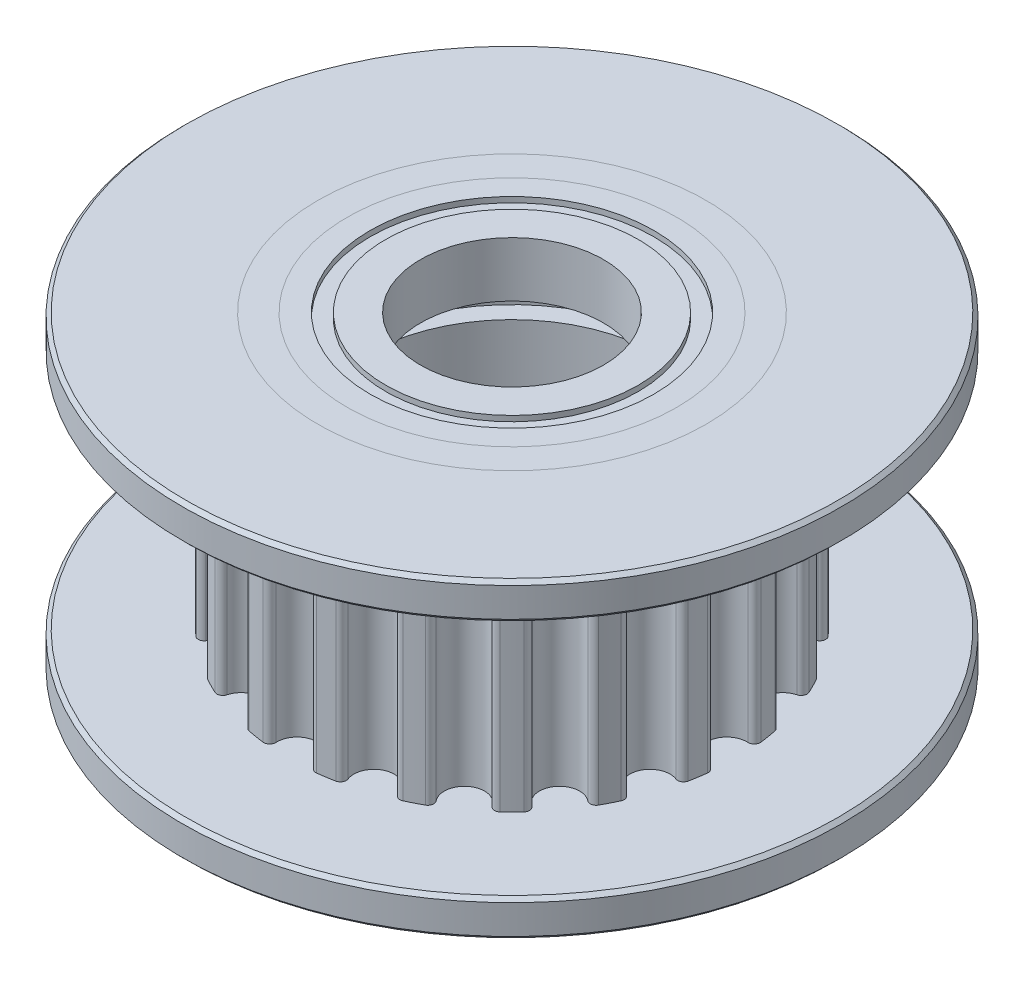
SolidWorks part; units mm, degrees
material "1060 Alloy"
ref_plane "Přední rovina" through (0, 0, 0) normal (0, 0, 1) x (1, 0, 0)
ref_plane "Horní rovina" through (0, 0, 0) normal (0, 1, 0) x (1, 0, 0)
ref_plane "Pravá rovina" through (0, 0, 0) normal (1, 0, 0) x (0, 0, -1)
sketch "Skica1" plane through (0, 0, 0) normal (0, 0, 1) x (1, 0, 0)
  line L0 (0, 0) -> (0, 8.5) construction
  line L1 (4.5, 8.5) -> (5.3, 8.5)
  line L2 (5.3, 8.5) -> (5.3, 7.5)
  line L3 (5.3, 7.5) -> (9, 7.5)
  line L4 (9, 7.5) -> (9, 1)
  line L5 (4.5, 0) -> (5.3, 0)
  line L6 (5.3, 0) -> (5.3, 1)
  line L7 (5.3, 1) -> (9, 1)
  line L8 (4.5, 3) -> (4, 3)
  line L9 (4.5, 3) -> (4.5, 0)
  line L10 (4.5, 8.5) -> (4.5, 5.5)
  line L11 (4.5, 5.5) -> (4, 5.5)
  line L12 (4, 5.5) -> (4, 3)
  dimension "D1" = 6.5
  dimension "D2" = 2.5
  dimension "D3" = 3
  dimension "D4" = 9
  dimension "D5" = 4.5
  dimension "D6" = 5.3
  dimension "D7" = 8.5
revolve "Rotovat1" add sketch "Skica1" angle 360 about L0
sketch "Skica2" plane through (0, 7.5, 0) normal (0, 1, 0) x (1, 0, 0)
  arc A0 (-0.5492, 5.8991) -> (0.5492, 5.8991) centre (0, 5.87) ccw
  arc A1 (-0.5492, 5.8991) -> (-0.7281, 6.0665) centre (-0.709, 5.9076) ccw
  arc A2 (0.7281, 6.0665) -> (0.5492, 5.8991) centre (0.709, 5.9076) ccw
  arc A3 (1.1822, 5.9945) -> (0.7281, 6.0665) centre (0, 0) ccw
  arc A4 (1.3006, 5.7801) -> (2.3453, 5.4407) centre (1.8139, 5.5827) ccw
  arc A5 (1.3006, 5.7801) -> (1.1822, 5.9945) centre (1.1512, 5.8376) ccw
  arc A6 (2.5671, 5.5446) -> (2.3453, 5.4407) centre (2.4999, 5.3994) ccw
  arc A7 (2.9768, 5.3358) -> (2.5671, 5.5446) centre (0, 0) ccw
  arc A8 (3.0231, 5.0953) -> (3.9118, 4.4497) centre (3.4503, 4.7489) ccw
  arc A9 (3.0231, 5.0953) -> (2.9768, 5.3358) centre (2.8988, 5.1961) ccw
  arc A10 (4.1548, 4.4799) -> (3.9118, 4.4497) centre (4.046, 4.3626) ccw
  arc A11 (4.4799, 4.1548) -> (4.1548, 4.4799) centre (0, 0) ccw
  arc A12 (4.4497, 3.9118) -> (5.0953, 3.0231) centre (4.7489, 3.4503) ccw
  arc A13 (4.4497, 3.9118) -> (4.4799, 4.1548) centre (4.3626, 4.046) ccw
  arc A14 (5.3358, 2.9768) -> (5.0953, 3.0231) centre (5.1961, 2.8988) ccw
  arc A15 (5.5446, 2.5671) -> (5.3358, 2.9768) centre (0, 0) ccw
  arc A16 (5.4407, 2.3453) -> (5.7801, 1.3006) centre (5.5827, 1.8139) ccw
  arc A17 (5.4407, 2.3453) -> (5.5446, 2.5671) centre (5.3994, 2.4999) ccw
  arc A18 (5.9945, 1.1822) -> (5.7801, 1.3006) centre (5.8376, 1.1512) ccw
  arc A19 (6.0665, 0.7281) -> (5.9945, 1.1822) centre (0, 0) ccw
  arc A20 (5.8991, 0.5492) -> (5.8991, -0.5492) centre (5.87, 0) ccw
  arc A21 (5.8991, 0.5492) -> (6.0665, 0.7281) centre (5.9076, 0.709) ccw
  arc A22 (6.0665, -0.7281) -> (5.8991, -0.5492) centre (5.9076, -0.709) ccw
  arc A23 (5.9945, -1.1822) -> (6.0665, -0.7281) centre (0, 0) ccw
  arc A24 (5.7801, -1.3006) -> (5.4407, -2.3453) centre (5.5827, -1.8139) ccw
  arc A25 (5.7801, -1.3006) -> (5.9945, -1.1822) centre (5.8376, -1.1512) ccw
  arc A26 (5.5446, -2.5671) -> (5.4407, -2.3453) centre (5.3994, -2.4999) ccw
  arc A27 (5.3358, -2.9768) -> (5.5446, -2.5671) centre (0, 0) ccw
  arc A28 (5.0953, -3.0231) -> (4.4497, -3.9118) centre (4.7489, -3.4503) ccw
  arc A29 (5.0953, -3.0231) -> (5.3358, -2.9768) centre (5.1961, -2.8988) ccw
  arc A30 (4.4799, -4.1548) -> (4.4497, -3.9118) centre (4.3626, -4.046) ccw
  arc A31 (4.1548, -4.4799) -> (4.4799, -4.1548) centre (0, 0) ccw
  arc A32 (3.9118, -4.4497) -> (3.0231, -5.0953) centre (3.4503, -4.7489) ccw
  arc A33 (3.9118, -4.4497) -> (4.1548, -4.4799) centre (4.046, -4.3626) ccw
  arc A34 (2.9768, -5.3358) -> (3.0231, -5.0953) centre (2.8988, -5.1961) ccw
  arc A35 (2.5671, -5.5446) -> (2.9768, -5.3358) centre (0, 0) ccw
  arc A36 (2.3453, -5.4407) -> (1.3006, -5.7801) centre (1.8139, -5.5827) ccw
  arc A37 (2.3453, -5.4407) -> (2.5671, -5.5446) centre (2.4999, -5.3994) ccw
  arc A38 (1.1822, -5.9945) -> (1.3006, -5.7801) centre (1.1512, -5.8376) ccw
  arc A39 (0.7281, -6.0665) -> (1.1822, -5.9945) centre (0, 0) ccw
  arc A40 (0.5492, -5.8991) -> (-0.5492, -5.8991) centre (0, -5.87) ccw
  arc A41 (0.5492, -5.8991) -> (0.7281, -6.0665) centre (0.709, -5.9076) ccw
  arc A42 (-0.7281, -6.0665) -> (-0.5492, -5.8991) centre (-0.709, -5.9076) ccw
  arc A43 (-1.1822, -5.9945) -> (-0.7281, -6.0665) centre (0, 0) ccw
  arc A44 (-1.3006, -5.7801) -> (-2.3453, -5.4407) centre (-1.8139, -5.5827) ccw
  arc A45 (-1.3006, -5.7801) -> (-1.1822, -5.9945) centre (-1.1512, -5.8376) ccw
  arc A46 (-2.5671, -5.5446) -> (-2.3453, -5.4407) centre (-2.4999, -5.3994) ccw
  arc A47 (-2.9768, -5.3358) -> (-2.5671, -5.5446) centre (0, 0) ccw
  arc A48 (-3.0231, -5.0953) -> (-3.9118, -4.4497) centre (-3.4503, -4.7489) ccw
  arc A49 (-3.0231, -5.0953) -> (-2.9768, -5.3358) centre (-2.8988, -5.1961) ccw
  arc A50 (-4.1548, -4.4799) -> (-3.9118, -4.4497) centre (-4.046, -4.3626) ccw
  arc A51 (-4.4799, -4.1548) -> (-4.1548, -4.4799) centre (0, 0) ccw
  arc A52 (-4.4497, -3.9118) -> (-5.0953, -3.0231) centre (-4.7489, -3.4503) ccw
  arc A53 (-4.4497, -3.9118) -> (-4.4799, -4.1548) centre (-4.3626, -4.046) ccw
  arc A54 (-5.3358, -2.9768) -> (-5.0953, -3.0231) centre (-5.1961, -2.8988) ccw
  arc A55 (-5.5446, -2.5671) -> (-5.3358, -2.9768) centre (0, 0) ccw
  arc A56 (-5.4407, -2.3453) -> (-5.7801, -1.3006) centre (-5.5827, -1.8139) ccw
  arc A57 (-5.4407, -2.3453) -> (-5.5446, -2.5671) centre (-5.3994, -2.4999) ccw
  arc A58 (-5.9945, -1.1822) -> (-5.7801, -1.3006) centre (-5.8376, -1.1512) ccw
  arc A59 (-6.0665, -0.7281) -> (-5.9945, -1.1822) centre (0, 0) ccw
  arc A60 (-5.8991, -0.5492) -> (-5.8991, 0.5492) centre (-5.87, 0) ccw
  arc A61 (-5.8991, -0.5492) -> (-6.0665, -0.7281) centre (-5.9076, -0.709) ccw
  arc A62 (-6.0665, 0.7281) -> (-5.8991, 0.5492) centre (-5.9076, 0.709) ccw
  arc A63 (-5.9945, 1.1822) -> (-6.0665, 0.7281) centre (0, 0) ccw
  arc A64 (-5.7801, 1.3006) -> (-5.4407, 2.3453) centre (-5.5827, 1.8139) ccw
  arc A65 (-5.7801, 1.3006) -> (-5.9945, 1.1822) centre (-5.8376, 1.1512) ccw
  arc A66 (-5.5446, 2.5671) -> (-5.4407, 2.3453) centre (-5.3994, 2.4999) ccw
  arc A67 (-5.3358, 2.9768) -> (-5.5446, 2.5671) centre (0, 0) ccw
  arc A68 (-5.0953, 3.0231) -> (-4.4497, 3.9118) centre (-4.7489, 3.4503) ccw
  arc A69 (-5.0953, 3.0231) -> (-5.3358, 2.9768) centre (-5.1961, 2.8988) ccw
  arc A70 (-4.4799, 4.1548) -> (-4.4497, 3.9118) centre (-4.3626, 4.046) ccw
  arc A71 (-4.1548, 4.4799) -> (-4.4799, 4.1548) centre (0, 0) ccw
  arc A72 (-3.9118, 4.4497) -> (-3.0231, 5.0953) centre (-3.4503, 4.7489) ccw
  arc A73 (-3.9118, 4.4497) -> (-4.1548, 4.4799) centre (-4.046, 4.3626) ccw
  arc A74 (-2.9768, 5.3358) -> (-3.0231, 5.0953) centre (-2.8988, 5.1961) ccw
  arc A75 (-2.5671, 5.5446) -> (-2.9768, 5.3358) centre (0, 0) ccw
  arc A76 (-2.3453, 5.4407) -> (-1.3006, 5.7801) centre (-1.8139, 5.5827) ccw
  arc A77 (-2.3453, 5.4407) -> (-2.5671, 5.5446) centre (-2.4999, 5.3994) ccw
  arc A78 (-1.1822, 5.9945) -> (-1.3006, 5.7801) centre (-1.1512, 5.8376) ccw
  arc A79 (-0.7281, 6.0665) -> (-1.1822, 5.9945) centre (0, 0) ccw
  circle A81 centre (0, 0) radius 9
  point P3 (0, 0)
  point P143 (0, 0)
  dimension "D1" = 18
  dimension "D2" = 6.11
  dimension "D4" = 0.55
  dimension "D5" = 0.16
  dimension "D3" = 5.87
  dimension "D6" = 5.95
  dimension "D7" = 1.8365
  dimension "D8" = 0.4478
extrude "Odebrat vysunutím1" cut sketch "Skica2" against normal blind 6.5
sketch "Skica3" plane through (0, 7.5, 0) normal (0, 1, 0) x (1, 0, 0)
  circle A0 centre (0, 0) radius 9
  circle A1 centre (0, 0) radius 5.3
  dimension "D1" = 18
  dimension "D2" = 10.6
extrude "Přidat vysunutím1" add sketch "Skica3" along normal blind 1 separate body
sketch "Skica5" plane through (0, 1, 0) normal (0, -1, 0) x (1, 0, 0)
  circle A0 centre (0, 0) radius 9
  circle A1 centre (0, 0) radius 5.3
  dimension "D1" = 10.6
  dimension "D2" = 18
extrude "Přidat vysunutím2" add sketch "Skica5" along normal blind 1 separate body
chamfer "Zkosení1" distance 0.1 angle 45 2 edges at (-9, 7.5, 0) (-9, 8.5, 0)
chamfer "Zkosení2" distance 0.1 angle 45 2 edges at (9, 1, 0) (9, 0, 0)
sketch "Sketch1" plane through (0, 0, 0) normal (0, -1, 0) x (1, 0, 0)
  circle A0 centre (0, 0) radius 4.5
  circle A2 centre (0, 0) radius 4.5 construction
  circle A3 centre (0, 0) radius 2.5
  dimension "D1" = 5
extrude "Boss-Extrude1" add sketch "Sketch1" against normal blind 1.5 separate body
sketch "Sketch3" plane through (0, 0, 0) normal (0, -1, 0) x (1, 0, 0)
  circle A0 centre (0, 0) radius 3.875
  circle A1 centre (0, 0) radius 3.45
  dimension "D1" = 7.75
  dimension "D2" = 6.9
extrude "Cut-Extrude1" cut sketch "Sketch3" against normal blind 0.15
ref_plane "Plane1" through (0, 4.25, 0) normal (0, 1, 0) x (1, 0, 0)
mirror "Mirror3" about plane through (0, 4.25, 0) normal (0, 1, 0) of bodies 107
